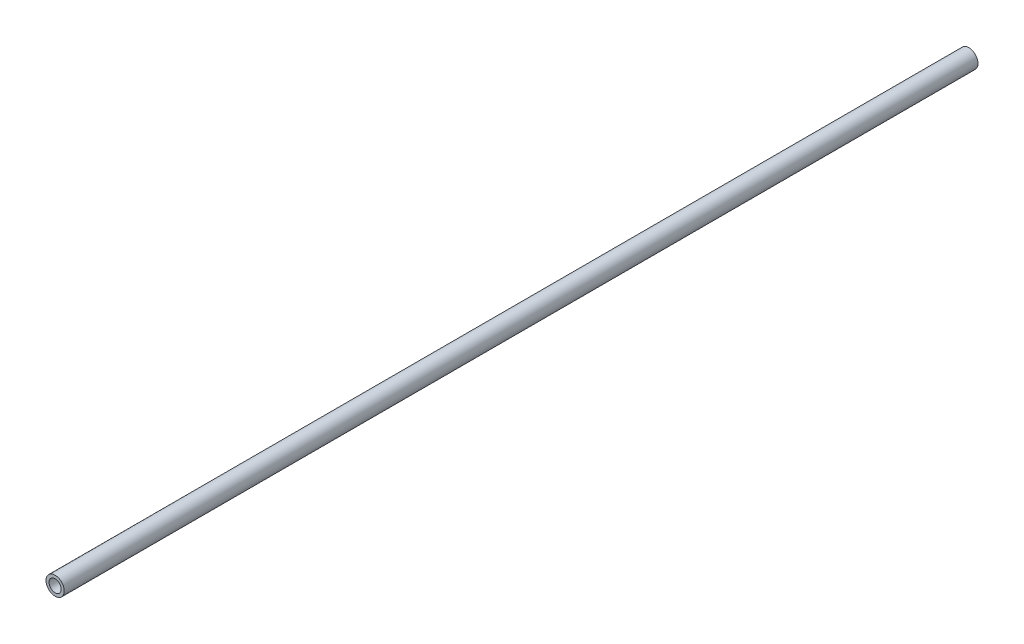
SolidWorks part; units mm, degrees
material "PVC Rigid"
ref_plane "Front Plane" through (0, 0, 0) normal (0, 0, 1) x (1, 0, 0)
ref_plane "Top Plane" through (0, 0, 0) normal (0, 1, 0) x (1, 0, 0)
ref_plane "Right Plane" through (0, 0, 0) normal (1, 0, 0) x (0, 0, -1)
sketch "Sketch2" plane through (0, 0, 0) normal (0, 0, 1) x (1, 0, 0)
  circle A0 centre (0, 0) radius 7.62
  circle A2 centre (0, 0) radius 5.08
  dimension "D1" = 15.24
  dimension "D2" = 10.16
extrude "Boss-Extrude1" add sketch "Sketch2" along normal blind 762
